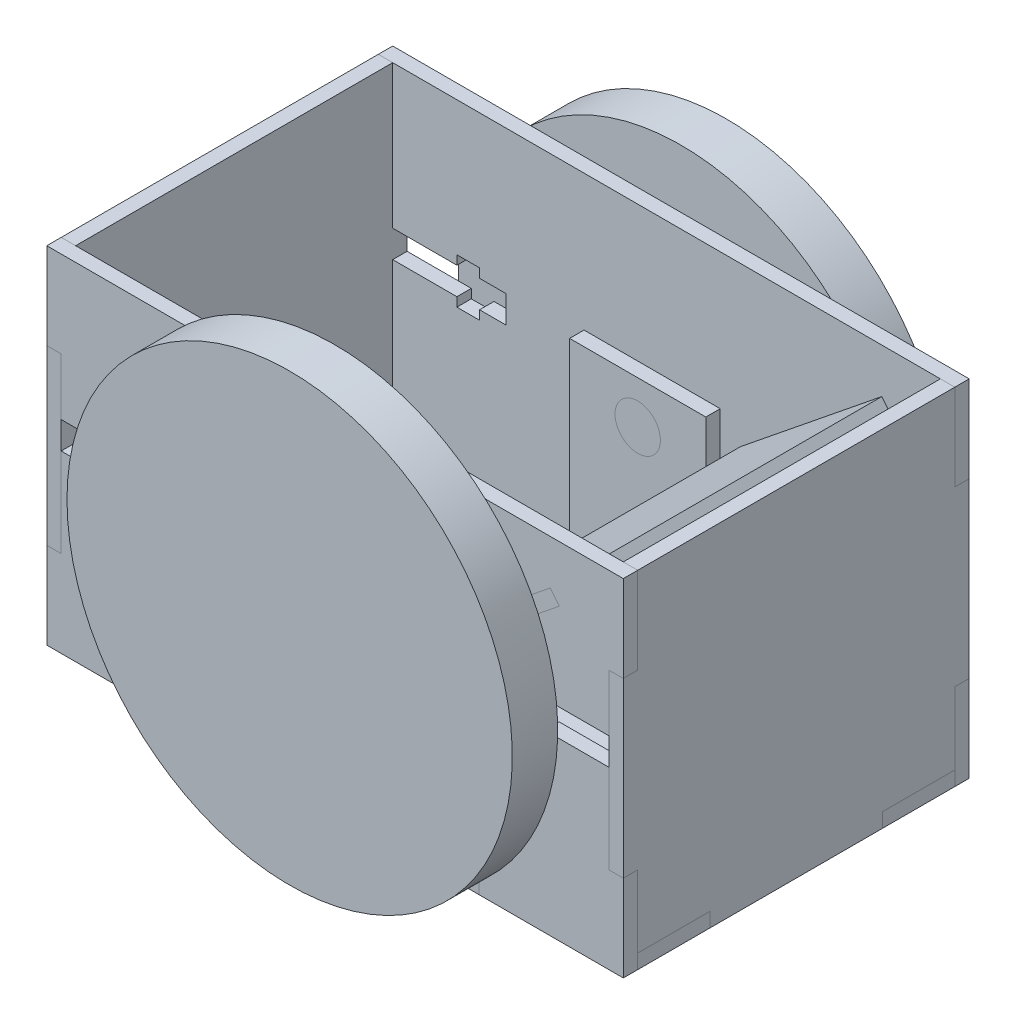
SolidWorks part; units mm, degrees
ref_plane "Front Plane" through (0, 0, 0) normal (0, 0, 1) x (1, 0, 0)
ref_plane "Top Plane" through (0, 0, 0) normal (0, 1, 0) x (1, 0, 0)
ref_plane "Right Plane" through (0, 0, 0) normal (1, 0, 0) x (0, 0, -1)
sketch "Sketch1" plane through (0, 0, 0) normal (0, 1, 0) x (1, 0, 0)
  line L0 (0, 0) -> (24.4942, 0) construction
  line L1 (-31.75, -38.1) -> (31.75, -38.1)
  line L2 (-63.5, -34.925) -> (-63.5, -19.05)
  line L3 (-31.75, 38.1) -> (31.75, 38.1)
  line L4 (63.5, -34.925) -> (63.5, -19.05)
  line L5 (-58.2083, -34.925) -> (58.2083, 34.925) construction
  line L6 (-58.2083, 34.925) -> (58.2083, -34.925) construction
  line L7 (-53.5, 1.5875) -> (-33.5, 1.5875)
  line L8 (-53.5, 1.5875) -> (-53.5, -1.5875)
  line L9 (-53.5, -1.5875) -> (-33.5, -1.5875)
  line L10 (-33.5, 1.5875) -> (-33.5, -1.5875)
  line L11 (-53.5, 1.5875) -> (-33.5, -1.5875) construction
  line L12 (-53.5, -1.5875) -> (-33.5, 1.5875) construction
  line L13 (-45.0875, -10) -> (-41.9125, -10)
  line L14 (-45.0875, -10) -> (-45.0875, 10)
  line L15 (-45.0875, 10) -> (-41.9125, 10)
  line L16 (-41.9125, -10) -> (-41.9125, 10)
  line L17 (-45.0875, -10) -> (-41.9125, 10) construction
  line L18 (-45.0875, 10) -> (-41.9125, -10) construction
  line L19 (-15, 31.75) -> (15, 31.75)
  line L20 (-15, 31.75) -> (-15, 28.575)
  line L21 (-15, 28.575) -> (15, 28.575)
  line L22 (15, 31.75) -> (15, 28.575)
  line L23 (-15, 31.75) -> (15, 28.575) construction
  line L24 (-15, 28.575) -> (15, 31.75) construction
  line L25 (-15, -28.575) -> (15, -28.575)
  line L26 (15, -31.75) -> (15, -28.575)
  line L27 (-15, -31.75) -> (15, -31.75)
  line L28 (-15, -31.75) -> (-15, -28.575)
  line L29 (-15, -28.575) -> (15, -31.75) construction
  line L30 (-15, -31.75) -> (15, -28.575) construction
  line L31 (0, 12.0256) -> (0, -12.0256) construction
  line L37 (63.5, -34.925) -> (44.3333, -34.925)
  line L38 (31.75, -38.1) -> (31.75, -34.925)
  line L39 (40.3333, -34.925) -> (31.75, -34.925)
  line L41 (40.3333, -34.925) -> (40.3333, -26.7608)
  line L42 (40.3333, -17.0144) -> (44.3333, -17.0144)
  line L43 (44.3333, -34.925) -> (44.3333, -26.6)
  line L44 (-40.3333, -22.7608) -> (-40.3333, -17.0144)
  line L45 (-44.3333, -22.7608) -> (-47.3333, -22.7608)
  line L46 (37.3333, -26.7608) -> (40.3333, -26.7608)
  line L47 (37.3333, -26.7608) -> (37.3333, -22.7608)
  line L48 (37.3333, -22.7608) -> (40.3333, -22.7608)
  line L49 (47.3333, -26.7608) -> (47.3333, -22.7608)
  line L50 (44.3333, -22.7608) -> (44.3333, -17.0144)
  line L51 (-44.3333, -26.7608) -> (-47.3333, -26.7608)
  line L52 (-44.3333, -22.7608) -> (-44.3333, -17.0144)
  line L53 (44.3333, -26.7608) -> (47.3333, -26.7608)
  line L54 (44.3333, -22.7608) -> (47.3333, -22.7608)
  line L55 (40.3333, -22.7608) -> (40.3333, -17.0144)
  line L56 (-47.3333, -26.7608) -> (-47.3333, -22.7608)
  line L57 (-37.3333, -22.7608) -> (-40.3333, -22.7608)
  line L58 (-37.3333, -26.7608) -> (-37.3333, -22.7608)
  line L59 (-37.3333, -26.7608) -> (-40.3333, -26.7608)
  line L60 (-44.3333, -34.925) -> (-44.3333, -26.6)
  line L61 (-40.3333, -17.0144) -> (-44.3333, -17.0144)
  line L62 (-40.3333, -34.925) -> (-40.3333, -26.7608)
  line L63 (-40.3333, -34.925) -> (-31.75, -34.925)
  line L64 (-31.75, -38.1) -> (-31.75, -34.925)
  line L65 (-63.5, -34.925) -> (-44.3333, -34.925)
  line L66 (60.325, -19.05) -> (60.325, 19.05)
  line L67 (63.5, -19.05) -> (60.325, -19.05)
  line L68 (-15, 31.75) -> (15, 28.575) construction
  line L69 (-15, 28.575) -> (15, 31.75) construction
  line L70 (63.5, 19.05) -> (60.325, 19.05)
  line L71 (63.5, 19.05) -> (63.5, 34.925)
  line L72 (-63.5, 34.925) -> (-44.3333, 34.925)
  line L73 (-31.75, 38.1) -> (-31.75, 34.925)
  line L74 (-40.3333, 34.925) -> (-31.75, 34.925)
  line L75 (-40.3333, 34.925) -> (-40.3333, 26.7608)
  line L76 (-40.3333, 17.0144) -> (-44.3333, 17.0144)
  line L77 (-44.3333, 34.925) -> (-44.3333, 26.6)
  line L78 (-37.3333, 26.7608) -> (-40.3333, 26.7608)
  line L79 (-37.3333, 26.7608) -> (-37.3333, 22.7608)
  line L80 (-37.3333, 22.7608) -> (-40.3333, 22.7608)
  line L81 (-47.3333, 26.7608) -> (-47.3333, 22.7608)
  line L82 (40.3333, 22.7608) -> (40.3333, 17.0144)
  line L83 (44.3333, 22.7608) -> (47.3333, 22.7608)
  line L84 (44.3333, 26.7608) -> (47.3333, 26.7608)
  line L85 (-44.3333, 22.7608) -> (-44.3333, 17.0144)
  line L86 (-44.3333, 26.7608) -> (-47.3333, 26.7608)
  line L87 (44.3333, 22.7608) -> (44.3333, 17.0144)
  line L88 (47.3333, 26.7608) -> (47.3333, 22.7608)
  line L89 (37.3333, 22.7608) -> (40.3333, 22.7608)
  line L90 (37.3333, 26.7608) -> (37.3333, 22.7608)
  line L91 (37.3333, 26.7608) -> (40.3333, 26.7608)
  line L92 (-44.3333, 22.7608) -> (-47.3333, 22.7608)
  line L93 (-40.3333, 22.7608) -> (-40.3333, 17.0144)
  line L94 (44.3333, 34.925) -> (44.3333, 26.6)
  line L95 (40.3333, 17.0144) -> (44.3333, 17.0144)
  line L96 (40.3333, 34.925) -> (40.3333, 26.7608)
  line L97 (40.3333, 34.925) -> (31.75, 34.925)
  line L98 (31.75, 38.1) -> (31.75, 34.925)
  line L99 (63.5, 34.925) -> (44.3333, 34.925)
  line L102 (-15, 31.75) -> (-15, 28.575)
  line L103 (-15, 31.75) -> (15, 31.75)
  line L104 (15, 31.75) -> (15, 28.575)
  line L105 (-15, 28.575) -> (15, 28.575)
  line L106 (-31.75, 38.1) -> (31.75, 38.1)
  line L107 (-63.5, 19.05) -> (-63.5, 34.925)
  line L108 (-63.5, -19.05) -> (-60.325, -19.05)
  line L110 (-63.5, 19.05) -> (-60.325, 19.05)
  line L111 (-60.325, -19.05) -> (-60.325, 19.05)
  point P0 (0, 0)
  point P6 (-43.5, 0)
  point P11 (-43.5, 0)
  point P16 (0, 30.1625)
  point P31 (42.3333, -34.925)
  point P33 (-42.3333, -24.7608)
  point P35 (-42.3333, -34.925)
  point P36 (42.3333, -24.7608)
  point P99 (42.3333, 24.7608)
  point P100 (-42.3333, 34.925)
  point P101 (-42.3333, 24.7608)
  point P102 (42.3333, 34.925)
  point P103 (-63.5, 0)
  dimension "D3" = 3.175
  dimension "D4" = 20
  dimension "D5" = 20
  dimension "D6" = 30
  dimension "D7" = 6.35
  dimension "D8" = 3.175
  dimension "D9" = 3.175
  dimension "D10" = 31.75
  dimension "D11" = 4
  dimension "D12" = 10
  dimension "D13" = 4
  dimension "D14" = 3.175
extrude "Boss-Extrude1" add sketch "Sketch1" along normal blind 3.175 contours L1 L4 L3 L2 L16 L13 L14 L9 L8 L7 L15 L10 L19 L22 L21 L20 L27 L28 L25 L26
sketch "Sketch2" plane through (0, 0, 38.1) normal (0, 0, 1) x (1, 0, 0)
  line L4 (-63.5, 0) -> (-31.75, 0)
  line L5 (-63.5, 0) -> (-63.5, 19.05)
  line L6 (63.5, 0) -> (63.5, 19.05)
  line L7 (-63.5, 76.2) -> (63.5, 76.2)
  line L8 (-31.75, 0) -> (31.75, 0)
  line L9 (31.75, 0) -> (31.75, 3.175)
  line L10 (31.75, 3.175) -> (-31.75, 3.175)
  line L11 (-31.75, 3.175) -> (-31.75, 0)
  line L13 (31.75, 0) -> (31.75, 3.175)
  line L14 (31.75, 3.175) -> (3, 3.175)
  line L15 (-31.75, 3.175) -> (-31.75, 0)
  line L16 (31.75, 0) -> (63.5, 0)
  line L17 (3, 17.315) -> (5, 17.315)
  line L19 (-3, 3.175) -> (-3, 17.315)
  line L20 (-3, 28.175) -> (3, 28.175)
  line L21 (3, 3.175) -> (3, 17.315)
  line L22 (-5, 22.315) -> (-3, 22.315)
  line L23 (-5, 22.315) -> (-5, 17.315)
  line L24 (-5, 17.315) -> (-3, 17.315)
  line L25 (5, 22.315) -> (5, 17.315)
  line L26 (49.4181, 63.901) -> (18.2884, 38.7825)
  line L27 (49.4181, 63.901) -> (47.4244, 66.372)
  line L28 (18.2884, 38.7825) -> (16.2946, 41.2535)
  line L29 (47.4244, 66.372) -> (16.2946, 41.2535)
  line L30 (3, 22.315) -> (5, 22.315)
  line L31 (-3, 22.315) -> (-3, 28.175)
  line L32 (3, 22.315) -> (3, 28.175)
  line L33 (49.4181, 63.901) -> (16.2946, 41.2535) construction
  line L34 (18.2884, 38.7825) -> (47.4244, 66.372) construction
  line L35 (-31.75, 0) -> (31.75, 0) construction
  line L36 (-3, 3.175) -> (-31.75, 3.175)
  line L37 (-63.5, 57.15) -> (-63.5, 76.2)
  line L38 (-63.5, 57.15) -> (-60.325, 57.15)
  line L40 (-63.5, 19.05) -> (-60.325, 19.05)
  line L41 (-60.325, 57.15) -> (-60.325, 44.6222)
  line L42 (0, 0) -> (0, 19.815) construction
  line L43 (60.325, 57.15) -> (60.325, 19.05)
  line L44 (63.5, 19.05) -> (60.325, 19.05)
  line L45 (63.5, 57.15) -> (60.325, 57.15)
  line L46 (63.5, 57.15) -> (63.5, 76.2)
  line L47 (-60.325, 38.6222) -> (-60.325, 19.05)
  line L48 (-46.185, 38.6222) -> (-46.185, 36.6222)
  line L49 (-60.325, 44.6222) -> (-46.185, 44.6222)
  line L50 (-35.325, 44.6222) -> (-35.325, 38.6222)
  line L51 (-60.325, 38.6222) -> (-46.185, 38.6222)
  line L52 (-41.185, 46.6222) -> (-41.185, 44.6222)
  line L53 (-41.185, 46.6222) -> (-46.185, 46.6222)
  line L54 (-46.185, 46.6222) -> (-46.185, 44.6222)
  line L55 (-41.185, 36.6222) -> (-46.185, 36.6222)
  line L56 (-41.185, 38.6222) -> (-41.185, 36.6222)
  line L57 (-41.185, 44.6222) -> (-35.325, 44.6222)
  line L58 (-41.185, 38.6222) -> (-35.325, 38.6222)
  line L59 (63.4522, 41.6222) -> (43.6371, 41.6222) construction
  line L60 (-63.4522, 41.6222) -> (-43.6371, 41.6222) construction
  line L61 (41.185, 38.6222) -> (35.325, 38.6222)
  line L62 (41.185, 44.6222) -> (35.325, 44.6222)
  line L63 (41.185, 38.6222) -> (41.185, 36.6222)
  line L64 (41.185, 36.6222) -> (46.185, 36.6222)
  line L65 (46.185, 46.6222) -> (46.185, 44.6222)
  line L66 (41.185, 46.6222) -> (46.185, 46.6222)
  line L67 (41.185, 46.6222) -> (41.185, 44.6222)
  line L68 (60.325, 38.6222) -> (46.185, 38.6222)
  line L69 (35.325, 44.6222) -> (35.325, 38.6222)
  line L70 (60.325, 44.6222) -> (46.185, 44.6222)
  line L71 (46.185, 38.6222) -> (46.185, 36.6222)
  circle A0 centre (0, 40) radius 5
  point P16 (0, 19.815)
  point P28 (32.8564, 52.5772)
  point P51 (-43.6371, 41.6222)
  point P73 (43.6371, 41.6222)
  dimension "D7" = 10
  dimension "D1" = 0
  dimension "D2" = 76.2
  dimension "D3" = 6
  dimension "D4" = 25
  dimension "D5" = 10
  dimension "D6" = 5
  dimension "D8" = 3.175
  dimension "D9" = 40
  dimension "D10" = 40
  dimension "D11" = 38.1
  dimension "D12" = 3.175
  dimension "D13" = 6
  dimension "D14" = 25
  dimension "D15" = 10
  dimension "D16" = 5
extrude "Boss-Extrude2" add sketch "Sketch2" against normal up to surface (3.175 mm away) separate body contours A0 | L27 L29 L28 L26 | L71 L68 L43 L70 L65 L66 L67 L62 L69 L61 L63 L64
sketch "Sketch3" plane through (0, 0, -38.1) normal (0, 0, -1) x (-1, 0, 0)
  line L0 (-47.4244, 66.372) -> (-49.4181, 63.901) construction
  line L1 (-18.2884, 38.7825) -> (-49.4181, 63.901) construction
  line L2 (-16.2946, 41.2535) -> (-18.2884, 38.7825) construction
  line L3 (-16.2946, 41.2535) -> (-47.4244, 66.372) construction
  line L4 (-47.4244, 66.372) -> (-49.4181, 63.901)
  line L5 (-18.2884, 38.7825) -> (-49.4181, 63.901)
  line L6 (-16.2946, 41.2535) -> (-18.2884, 38.7825)
  line L7 (-16.2946, 41.2535) -> (-47.4244, 66.372)
  line L128 (-3, 28.175) -> (3, 28.175)
  line L129 (3, 28.175) -> (3, 22.315)
  line L130 (3, 22.315) -> (5, 22.315)
  line L131 (5, 22.315) -> (5, 17.315)
  line L156 (5, 17.315) -> (3, 17.315)
  line L157 (3, 17.315) -> (3, 3.175)
  line L158 (3, 3.175) -> (31.75, 3.175)
  line L159 (31.75, 3.175) -> (31.75, 0)
  line L160 (31.75, 0) -> (63.5, 0)
  line L161 (63.5, 0) -> (63.5, 19.05)
  line L162 (63.5, 19.05) -> (60.325, 19.05)
  line L163 (60.325, 19.05) -> (60.325, 38.6222)
  line L164 (60.325, 38.6222) -> (46.185, 38.6222)
  line L165 (46.185, 38.6222) -> (46.185, 36.6222)
  line L166 (46.185, 36.6222) -> (41.185, 36.6222)
  line L167 (41.185, 36.6222) -> (41.185, 38.6222)
  line L168 (41.185, 38.6222) -> (35.325, 38.6222)
  line L169 (35.325, 38.6222) -> (35.325, 44.6222)
  line L170 (35.325, 44.6222) -> (41.185, 44.6222)
  line L171 (41.185, 44.6222) -> (41.185, 46.6222)
  line L172 (41.185, 46.6222) -> (46.185, 46.6222)
  line L173 (46.185, 46.6222) -> (46.185, 44.6222)
  line L174 (46.185, 44.6222) -> (60.325, 44.6222)
  line L175 (60.325, 44.6222) -> (60.325, 57.15)
  line L176 (60.325, 57.15) -> (63.5, 57.15)
  line L177 (63.5, 57.15) -> (63.5, 76.2)
  line L178 (63.5, 76.2) -> (-63.5, 76.2)
  line L179 (-63.5, 76.2) -> (-63.5, 57.15)
  line L180 (-63.5, 57.15) -> (-60.325, 57.15)
  line L181 (-60.325, 57.15) -> (-60.325, 44.6222)
  line L182 (-60.325, 44.6222) -> (-46.185, 44.6222)
  line L183 (-46.185, 44.6222) -> (-46.185, 46.6222)
  line L184 (-46.185, 46.6222) -> (-41.185, 46.6222)
  line L185 (-41.185, 46.6222) -> (-41.185, 44.6222)
  line L186 (-41.185, 44.6222) -> (-35.325, 44.6222)
  line L187 (-35.325, 44.6222) -> (-35.325, 38.6222)
  line L188 (-35.325, 38.6222) -> (-41.185, 38.6222)
  line L189 (-41.185, 38.6222) -> (-41.185, 36.6222)
  line L190 (-41.185, 36.6222) -> (-46.185, 36.6222)
  line L191 (-46.185, 36.6222) -> (-46.185, 38.6222)
  line L192 (-46.185, 38.6222) -> (-60.325, 38.6222)
  line L193 (-60.325, 38.6222) -> (-60.325, 19.05)
  line L194 (-60.325, 19.05) -> (-63.5, 19.05)
  line L195 (-63.5, 19.05) -> (-63.5, 0)
  line L196 (-63.5, 0) -> (-31.75, 0)
  line L197 (-31.75, 0) -> (-31.75, 3.175)
  line L198 (-31.75, 3.175) -> (-3, 3.175)
  line L199 (-3, 3.175) -> (-3, 17.315)
  line L200 (-3, 17.315) -> (-5, 17.315)
  line L201 (-5, 17.315) -> (-5, 22.315)
  line L202 (-5, 22.315) -> (-3, 22.315)
  line L203 (-3, 22.315) -> (-3, 28.175)
  line L204 (-3, 28.175) -> (3, 28.175)
  line L205 (3, 28.175) -> (3, 22.315)
  line L206 (3, 22.315) -> (5, 22.315)
  line L207 (5, 22.315) -> (5, 17.315)
  line L208 (5, 17.315) -> (3, 17.315)
  line L209 (3, 17.315) -> (3, 3.175)
  line L210 (3, 3.175) -> (31.75, 3.175)
  line L211 (31.75, 3.175) -> (31.75, 0)
  line L212 (31.75, 0) -> (63.5, 0)
  line L213 (63.5, 0) -> (63.5, 19.05)
  line L214 (63.5, 19.05) -> (60.325, 19.05)
  line L215 (60.325, 19.05) -> (60.325, 38.6222)
  line L216 (60.325, 38.6222) -> (46.185, 38.6222)
  line L217 (46.185, 38.6222) -> (46.185, 36.6222)
  line L218 (46.185, 36.6222) -> (41.185, 36.6222)
  line L219 (41.185, 36.6222) -> (41.185, 38.6222)
  line L220 (41.185, 38.6222) -> (35.325, 38.6222)
  line L221 (35.325, 38.6222) -> (35.325, 44.6222)
  line L222 (35.325, 44.6222) -> (41.185, 44.6222)
  line L223 (41.185, 44.6222) -> (41.185, 46.6222)
  line L224 (41.185, 46.6222) -> (46.185, 46.6222)
  line L225 (46.185, 46.6222) -> (46.185, 44.6222)
  line L226 (46.185, 44.6222) -> (60.325, 44.6222)
  line L227 (60.325, 44.6222) -> (60.325, 57.15)
  line L228 (60.325, 57.15) -> (63.5, 57.15)
  line L229 (63.5, 57.15) -> (63.5, 76.2)
  line L230 (63.5, 76.2) -> (-63.5, 76.2)
  line L231 (-63.5, 76.2) -> (-63.5, 57.15)
  line L232 (-63.5, 57.15) -> (-60.325, 57.15)
  line L233 (-60.325, 57.15) -> (-60.325, 44.6222)
  line L234 (-60.325, 44.6222) -> (-46.185, 44.6222)
  line L235 (-46.185, 44.6222) -> (-46.185, 46.6222)
  line L236 (-46.185, 46.6222) -> (-41.185, 46.6222)
  line L237 (-41.185, 46.6222) -> (-41.185, 44.6222)
  line L238 (-41.185, 44.6222) -> (-35.325, 44.6222)
  line L239 (-35.325, 44.6222) -> (-35.325, 38.6222)
  line L240 (-35.325, 38.6222) -> (-41.185, 38.6222)
  line L241 (-41.185, 38.6222) -> (-41.185, 36.6222)
  line L242 (-41.185, 36.6222) -> (-46.185, 36.6222)
  line L243 (-46.185, 36.6222) -> (-46.185, 38.6222)
  line L244 (-46.185, 38.6222) -> (-60.325, 38.6222)
  line L245 (-60.325, 38.6222) -> (-60.325, 19.05)
  line L246 (-60.325, 19.05) -> (-63.5, 19.05)
  line L247 (-63.5, 19.05) -> (-63.5, 0)
  line L248 (-63.5, 0) -> (-31.75, 0)
  line L249 (-31.75, 0) -> (-31.75, 3.175)
  line L250 (-31.75, 3.175) -> (-3, 3.175)
  line L251 (-3, 3.175) -> (-3, 17.315)
  line L252 (-3, 17.315) -> (-5, 17.315)
  line L253 (-5, 17.315) -> (-5, 22.315)
  line L254 (-5, 22.315) -> (-3, 22.315)
  line L255 (-3, 22.315) -> (-3, 28.175)
  circle A0 centre (0, 40) radius 5 construction
  circle A1 centre (0, 40) radius 5
  dimension "D1" = 0
extrude "Boss-Extrude4" add sketch "Sketch3" against normal up to surface (3.175 mm away) separate body up to face at (-36.0417, 1.5875, -34.925)
sketch "Sketch4" plane through (-63.5, 0, 0) normal (-1, 0, 0) x (0, 0, 1)
  line L2 (38.1, 44.6222) -> (38.1, 57.15) construction
  line L3 (38.1, 57.15) -> (34.925, 57.15) construction
  line L6 (38.1, 38.6222) -> (38.1, 44.6222) construction
  line L9 (34.925, 19.05) -> (38.1, 19.05) construction
  line L10 (38.1, 19.05) -> (38.1, 38.6222) construction
  line L12 (-19.05, 0) -> (19.05, 0) construction
  line L13 (19.05, 0) -> (19.05, 3.175) construction
  line L15 (-19.05, 3.175) -> (-19.05, 0) construction
  line L18 (-38.1, 38.6222) -> (-38.1, 19.05) construction
  line L19 (-38.1, 19.05) -> (-34.925, 19.05) construction
  line L22 (-38.1, 44.6222) -> (-38.1, 38.6222) construction
  line L25 (-34.925, 57.15) -> (-38.1, 57.15) construction
  line L26 (-38.1, 57.15) -> (-38.1, 44.6222) construction
  line L28 (-19.05, 3.175) -> (-34.925, 3.175) construction
  line L31 (38.1, 44.6222) -> (38.1, 57.15)
  line L32 (38.1, 57.15) -> (34.925, 57.15)
  line L35 (38.1, 38.6222) -> (38.1, 44.6222)
  line L38 (34.925, 19.05) -> (38.1, 19.05)
  line L39 (38.1, 19.05) -> (38.1, 38.6222)
  line L41 (-19.05, 0) -> (19.05, 0)
  line L42 (19.05, 0) -> (19.05, 3.175)
  line L44 (-19.05, 3.175) -> (-19.05, 0)
  line L47 (-38.1, 38.6222) -> (-38.1, 19.05)
  line L48 (-38.1, 19.05) -> (-34.925, 19.05)
  line L51 (-38.1, 44.6222) -> (-38.1, 38.6222)
  line L54 (-34.925, 57.15) -> (-38.1, 57.15)
  line L55 (-38.1, 57.15) -> (-38.1, 44.6222)
  line L57 (-19.05, 3.175) -> (-34.925, 3.175)
  line L58 (-34.925, 57.15) -> (-34.925, 76.2)
  line L59 (-34.925, 76.2) -> (34.925, 76.2)
  line L60 (34.925, 76.2) -> (34.925, 57.15)
  line L61 (34.925, 19.05) -> (34.925, 3.175)
  line L62 (34.925, 3.175) -> (19.05, 3.175)
  line L63 (-34.925, 3.175) -> (-34.925, 19.05)
extrude "Boss-Extrude5" add sketch "Sketch4" against normal up to surface (3.175 mm away) separate body contours L51 L47 L48 L63 L57 L44 L41 L42 L62 L61 L38 L39 L35 L31 L32 L60 L59 L58 L54 L55 up to face at (-60.325, 50.8861, -36.5125)
sketch "Sketch5" plane through (63.5, 0, 0) normal (1, 0, 0) x (0, 0, -1)
  line L16 (38.1, 57.15) -> (34.925, 57.15)
  line L17 (34.925, 57.15) -> (34.925, 76.2)
  line L18 (34.925, 76.2) -> (-34.925, 76.2)
  line L19 (-34.925, 76.2) -> (-34.925, 57.15)
  line L20 (-34.925, 57.15) -> (-38.1, 57.15)
  line L21 (-38.1, 57.15) -> (-38.1, 19.05)
  line L22 (-38.1, 19.05) -> (-34.925, 19.05)
  line L23 (-34.925, 19.05) -> (-34.925, 3.175)
  line L24 (-34.925, 3.175) -> (-19.05, 3.175)
  line L25 (-19.05, 3.175) -> (-19.05, 0)
  line L26 (-19.05, 0) -> (19.05, 0)
  line L27 (19.05, 0) -> (19.05, 3.175)
  line L28 (19.05, 3.175) -> (34.925, 3.175)
  line L29 (34.925, 3.175) -> (34.925, 19.05)
  line L30 (34.925, 19.05) -> (38.1, 19.05)
  line L31 (38.1, 19.05) -> (38.1, 57.15)
  line L32 (38.1, 57.15) -> (34.925, 57.15)
  line L33 (34.925, 57.15) -> (34.925, 76.2)
  line L34 (34.925, 76.2) -> (-34.925, 76.2)
  line L35 (-34.925, 76.2) -> (-34.925, 57.15)
  line L36 (-34.925, 57.15) -> (-38.1, 57.15)
  line L37 (-38.1, 57.15) -> (-38.1, 19.05)
  line L38 (-38.1, 19.05) -> (-34.925, 19.05)
  line L39 (-34.925, 19.05) -> (-34.925, 3.175)
  line L40 (-34.925, 3.175) -> (-19.05, 3.175)
  line L41 (-19.05, 3.175) -> (-19.05, 0)
  line L42 (-19.05, 0) -> (19.05, 0)
  line L43 (19.05, 0) -> (19.05, 3.175)
  line L44 (19.05, 3.175) -> (34.925, 3.175)
  line L45 (34.925, 3.175) -> (34.925, 19.05)
  line L46 (34.925, 19.05) -> (38.1, 19.05)
  line L47 (38.1, 19.05) -> (38.1, 57.15)
  dimension "D1" = 0
extrude "Boss-Extrude6" add sketch "Sketch5" against normal up to surface (3.175 mm away) separate body up to face at (60.325, 1.5875, 0)
sketch "Sketch6" plane through (-11.7415, 14.5515, 0) normal (-0.628, 0.7782, 0) x (0.7782, 0.628, 0)
  line L1 (38.5868, 38.1) -> (78.5868, 38.1)
  line L2 (38.5868, 38.1) -> (38.5868, -38.1)
  line L3 (38.5868, -38.1) -> (78.5868, -38.1)
  line L4 (78.5868, 38.1) -> (78.5868, -38.1)
extrude "Boss-Extrude7" add sketch "Sketch6" along normal up to surface (3.175 mm away) separate body contours L2 L3 L4 L1 up to face at (31.8595, 53.8127, 36.5125)
sketch "Sketch7" plane through (0, 0, 31.75) normal (0, 0, -1) x (-1, 0, 0)
  line L9 (-15, 0) -> (15, 0)
  line L10 (-15, 0) -> (-15, 49.4336)
  line L11 (15, 0) -> (15, 49.4336)
  line L12 (-15, 49.4336) -> (15, 49.4336)
  line L13 (-24.1122, 3.175) -> (24.1122, 3.175)
  line L14 (-24.1122, 3.175) -> (-24.1122, 6.6019)
  line L15 (24.1122, 3.175) -> (24.1122, 6.6019)
  line L16 (-24.1122, 6.6019) -> (24.1122, 6.6019)
  line L17 (-3, 3.175) -> (-31.75, 3.175) construction
  line L18 (3, 3.175) -> (31.75, 3.175) construction
  circle A0 centre (0, 40) radius 5 construction
  circle A3 centre (0, 40) radius 5
  point P17 (0, 3.175)
extrude "Boss-Extrude8" add sketch "Sketch7" along normal up to surface (3.175 mm away) separate body contours A3 | L11 L12 L10 L9 | L16 L15 L13 L14
sketch "Sketch8" plane through (0, 0, -31.75) normal (0, 0, 1) x (1, 0, 0)
  line L12 (15, 6.6019) -> (15, 49.4336)
  line L13 (24.1122, 6.6019) -> (15, 6.6019)
  line L14 (24.1122, 3.175) -> (24.1122, 6.6019)
  line L15 (15, 3.175) -> (24.1122, 3.175)
  line L16 (15, 0) -> (15, 3.175)
  line L17 (-15, 0) -> (15, 0)
  line L18 (-15, 3.175) -> (-15, 0)
  line L19 (-24.1122, 3.175) -> (-15, 3.175)
  line L20 (-24.1122, 6.6019) -> (-24.1122, 3.175)
  line L21 (-15, 6.6019) -> (-24.1122, 6.6019)
  line L22 (-15, 49.4336) -> (-15, 6.6019)
  line L23 (15, 49.4336) -> (-15, 49.4336)
  line L24 (15, 6.6019) -> (15, 49.4336)
  line L25 (24.1122, 6.6019) -> (15, 6.6019)
  line L26 (24.1122, 3.175) -> (24.1122, 6.6019)
  line L27 (15, 3.175) -> (24.1122, 3.175)
  line L28 (15, 0) -> (15, 3.175)
  line L29 (-15, 0) -> (15, 0)
  line L30 (-15, 3.175) -> (-15, 0)
  line L31 (-24.1122, 3.175) -> (-15, 3.175)
  line L32 (-24.1122, 6.6019) -> (-24.1122, 3.175)
  line L33 (-15, 6.6019) -> (-24.1122, 6.6019)
  line L34 (-15, 49.4336) -> (-15, 6.6019)
  line L35 (15, 49.4336) -> (-15, 49.4336)
  circle A0 centre (0, 40) radius 5 construction
  circle A1 centre (0, 40) radius 5
  dimension "D1" = 0
extrude "Boss-Extrude9" add sketch "Sketch8" along normal up to surface (3.175 mm away) separate body up to face at (0, 1.5875, -28.575)
sketch "Sketch10" plane through (0, 0, 0) normal (1, 0, 0) x (0, 0, -1)
  line L1 (28.575, 40) -> (38.1, 40)
  line L2 (28.575, 45) -> (28.575, 35) construction
  line L4 (38.1, 35) -> (38.1, 45) construction
  line L5 (38.1, 35) -> (38.1, -9.0498)
  line L6 (38.1, -9.0498) -> (48.1, -9.0498)
  line L7 (48.1, -9.0498) -> (48.1, 40)
  line L8 (48.1, 40) -> (28.575, 40)
  line L10 (28.575, 40) -> (28.575, 35)
  line L11 (28.575, 6.6019) -> (28.575, 49.4336) construction
  line L12 (28.575, 35) -> (38.1, 35)
  dimension "D1" = 10
revolve "Revolve2" add sketch "Sketch10" angle 360 about L8
sketch "Sketch11" plane through (0, 3.175, 0) normal (0, 1, 0) x (1, 0, 0)
  line L0 (-45.0875, 10) -> (-41.9125, 10) construction
  line L1 (-45.0875, 1.5875) -> (-45.0875, 10) construction
  line L2 (-41.9125, 1.5875) -> (-41.9125, 10) construction
  line L3 (-41.9125, 1.5875) -> (-33.5, 1.5875) construction
  line L4 (-33.5, 1.5875) -> (-33.5, -1.5875) construction
  line L5 (-41.9125, -1.5875) -> (-33.5, -1.5875) construction
  line L6 (-41.9125, -10) -> (-41.9125, -1.5875) construction
  line L7 (-45.0875, -10) -> (-41.9125, -10) construction
  line L8 (-45.0875, -10) -> (-45.0875, -1.5875) construction
  line L9 (-53.5, -1.5875) -> (-45.0875, -1.5875) construction
  line L10 (-53.5, 1.5875) -> (-53.5, -1.5875) construction
  line L11 (-53.5, 1.5875) -> (-45.0875, 1.5875) construction
  line L12 (-45.0875, 10) -> (-41.9125, 10)
  line L13 (-45.0875, 1.5875) -> (-45.0875, 10)
  line L14 (-41.9125, 1.5875) -> (-41.9125, 10)
  line L15 (-41.9125, 1.5875) -> (-33.5, 1.5875)
  line L16 (-33.5, 1.5875) -> (-33.5, -1.5875)
  line L17 (-41.9125, -1.5875) -> (-33.5, -1.5875)
  line L18 (-41.9125, -10) -> (-41.9125, -1.5875)
  line L19 (-45.0875, -10) -> (-41.9125, -10)
  line L20 (-45.0875, -10) -> (-45.0875, -1.5875)
  line L21 (-53.5, -1.5875) -> (-45.0875, -1.5875)
  line L22 (-53.5, 1.5875) -> (-53.5, -1.5875)
  line L23 (-53.5, 1.5875) -> (-45.0875, 1.5875)
extrude "Boss-Extrude10" add sketch "Sketch11" against normal blind 14 separate body
ref_plane "Plane1" through (-43.5, 0, 0) normal (1, 0, 0) x (0, 0, -1)
sketch "Sketch13" plane through (-43.5, 0, 0) normal (1, 0, 0) x (0, 0, -1)
  line L0 (-10, -10.825) -> (-10, 3.175) construction
  line L1 (10, -10.825) -> (10, 3.175) construction
  line L2 (-0.0566, -10.8243) -> (-0.0566, -13.439)
  line L3 (-0.0566, -13.439) -> (11.6352, -13.439)
  line L4 (11.6352, -13.439) -> (11.6352, -5.6943)
  line L5 (11.6352, -5.6943) -> (10, -5.6943)
  arc A0 (-10, -5.4782) -> (10, -5.6943) centre (0.0749, 1.3403) ccw
revolve "Cut-Revolve2" cut sketch "Sketch13" angle 360 about L2
mirror "Mirror5" about plane through (0, 0, 0) normal (0, 0, 1) of bodies 110
